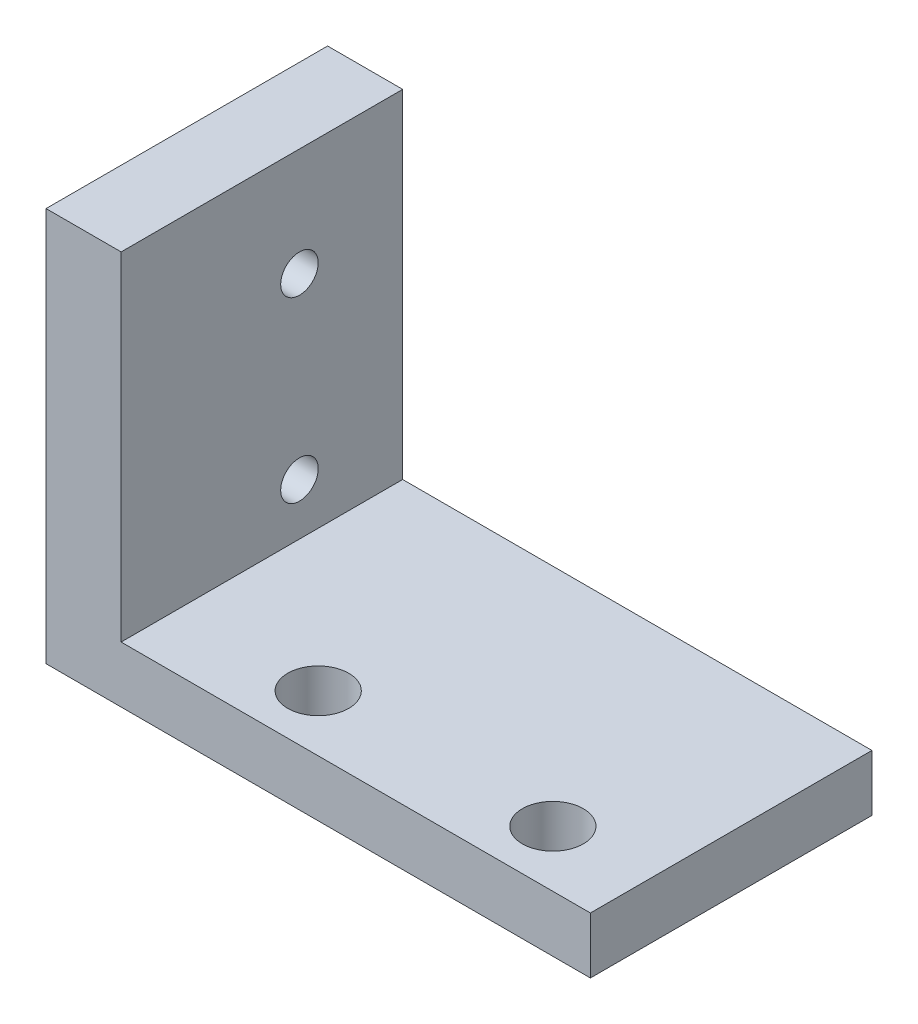
SolidWorks part; units mm, degrees
ref_plane "Front Plane" through (0, 0, 0) normal (0, 0, 1) x (1, 0, 0)
ref_plane "Top Plane" through (0, 0, 0) normal (0, 1, 0) x (1, 0, 0)
ref_plane "Right Plane" through (0, 0, 0) normal (1, 0, 0) x (0, 0, -1)
sketch "Sketch1" plane through (0, 0, 0) normal (0, 1, 0) x (1, 0, 0)
  line L0 (-14.5, 7.5) -> (14.5, -7.5) construction
  line L1 (-14.5, 7.5) -> (14.5, 7.5)
  line L2 (-14.5, 7.5) -> (-14.5, -7.5)
  line L3 (-14.5, -7.5) -> (14.5, -7.5)
  line L4 (14.5, 7.5) -> (14.5, -7.5)
  dimension "D1" = 29
  dimension "D2" = 15
extrude "Boss-Extrude1" add sketch "Sketch1" along normal blind 3
sketch "Sketch3" plane through (0, 3, 0) normal (0, 1, 0) x (1, 0, 0)
  line L0 (9.5, -4.5) -> (-3, -4.5) construction
  line L1 (14.5, -7.5) -> (14.5, 7.5) construction
  line L2 (-14.5, -7.5) -> (14.5, -7.5) construction
  circle A0 centre (-3, -4.5) radius 1.625
  circle A1 centre (9.5, -4.5) radius 1.625
  dimension "D2" = 3.25
  dimension "D3" = 5
  dimension "D1" = 12.5
  dimension "D4" = 3
extrude "Cut-Extrude2" cut sketch "Sketch3" against normal through all
sketch "Sketch4" plane through (0, 3, 0) normal (0, 1, 0) x (1, 0, 0)
  line L0 (-14.5, -7.5) -> (14.5, -7.5) construction
  line L1 (-14.5, 7.5) -> (-10.5, 7.5)
  line L2 (-14.5, 7.5) -> (-14.5, -7.5)
  line L3 (-14.5, -7.5) -> (-10.5, -7.5)
  line L4 (-10.5, 7.5) -> (-10.5, -7.5)
  dimension "D1" = 4
extrude "Boss-Extrude2" add sketch "Sketch4" along normal blind 18
sketch "Sketch5" plane through (-14.5, 0, 0) normal (-1, 0, 0) x (0, 0, 1)
  line L0 (7.5, 10.5) -> (-2, 10.5) construction
  line L1 (7.5, 21) -> (7.5, 0) construction
  line L2 (-2, 15.25) -> (-2, 5.75) construction
  circle A0 centre (-2, 15.25) radius 1
  circle A1 centre (-2, 5.75) radius 1
  dimension "D2" = 2
  dimension "D1" = 9.5
  dimension "D3" = 9.5
extrude "Cut-Extrude3" cut sketch "Sketch5" against normal blind 13
